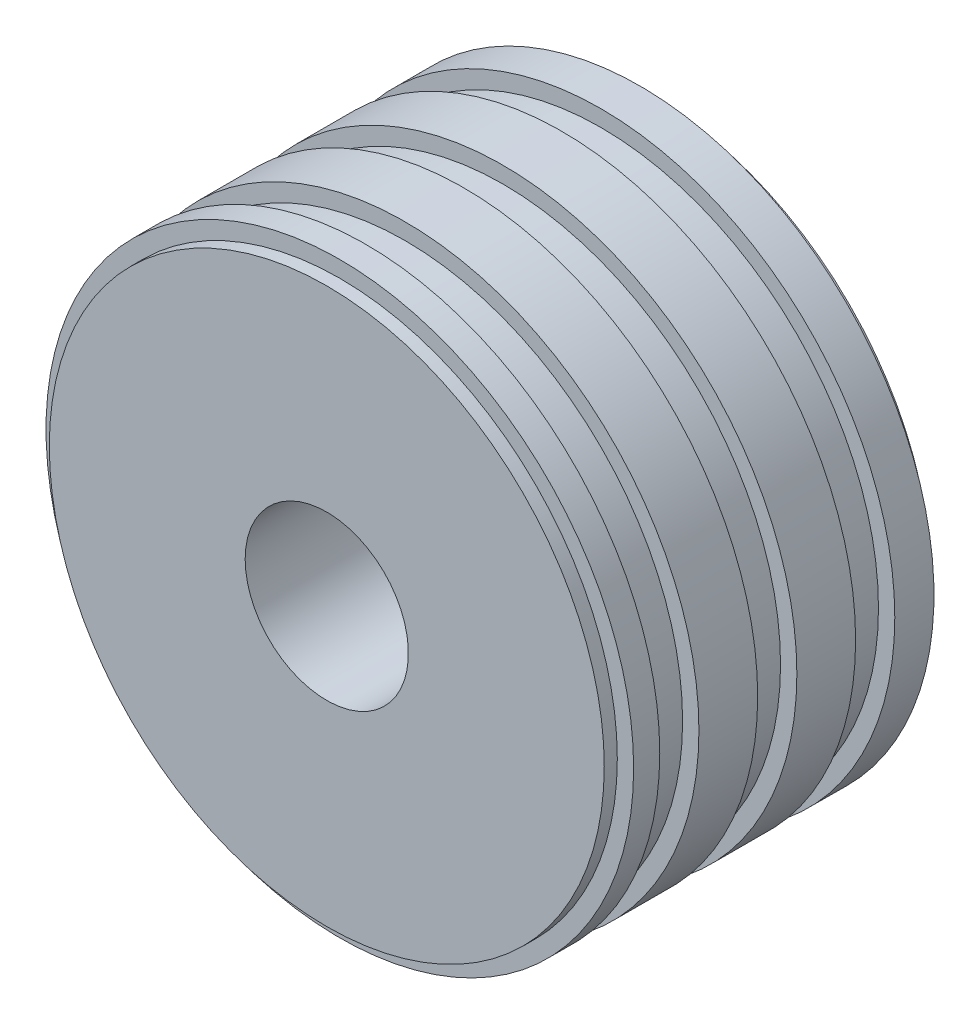
SolidWorks part; units mm, degrees
ref_plane "前视基准面" through (0, 0, 0) normal (0, 0, 1) x (1, 0, 0)
ref_plane "上视基准面" through (0, 0, 0) normal (0, 1, 0) x (1, 0, 0)
ref_plane "右视基准面" through (0, 0, 0) normal (1, 0, 0) x (0, 0, -1)
other "Configuration Table"
sketch "草图1" plane through (0, 0, 0) normal (0, 0, 1) x (1, 0, 0)
  circle A0 centre (0, 0) radius 45
  dimension "D1" = 90
extrude "凸台-拉伸1" add sketch "草图1" along normal blind 50
sketch "草图2" plane through (0, 0, 50) normal (0, 0, 1) x (1, 0, 0)
  circle A0 centre (0, 0) radius 45 construction
  circle A1 centre (0, 0) radius 45
  circle A2 centre (0, 0) radius 42.5
  dimension "D1" = 85
extrude "切除-拉伸1" cut sketch "草图2" against normal blind 6 from offset 6 offset against normal yes
pattern_linear "阵列(线性)1" count 3 spacing 15 along (0, 0, -1) of "切除-拉伸1"
sketch "草图3" plane through (0, 0, 50) normal (0, 0, 1) x (1, 0, 0)
  circle A0 centre (0, 0) radius 42.5
  circle A1 centre (0, 0) radius 45 construction
  circle A2 centre (0, 0) radius 45
  dimension "D1" = 85
extrude "切除-拉伸2" cut sketch "草图3" against normal blind 2
sketch "草图4" plane through (0, 0, 0) normal (0, 0, -1) x (-1, 0, 0)
  circle A0 centre (0, 0) radius 42.5
  circle A1 centre (0, 0) radius 45 construction
  circle A2 centre (0, 0) radius 45
  dimension "D1" = 85
extrude "切除-拉伸4" cut sketch "草图4" against normal blind 2
sketch "草图5" plane through (0, 0, 0) normal (0, 0, -1) x (-1, 0, 0)
  circle A0 centre (0, 0) radius 12.5
  dimension "D1" = 25
extrude "切除-拉伸5" cut sketch "草图5" against normal through all
